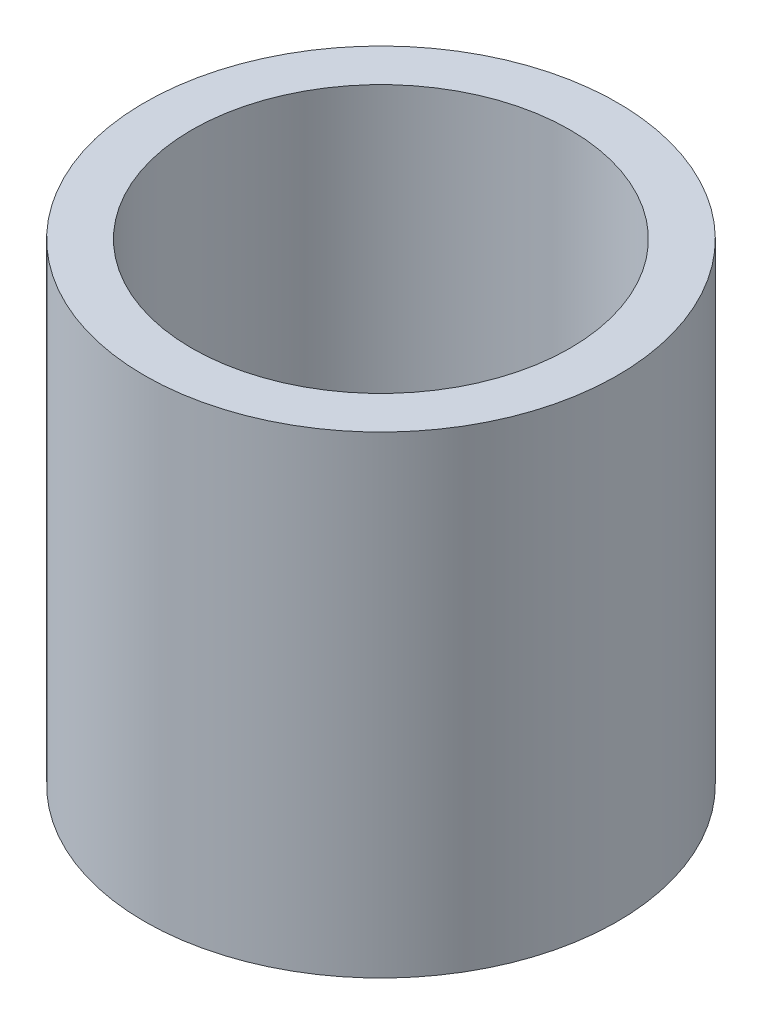
SolidWorks part; units mm, degrees
ref_plane "Front Plane" through (0, 0, 0) normal (0, 0, 1) x (1, 0, 0)
ref_plane "Top Plane" through (0, 0, 0) normal (0, 1, 0) x (1, 0, 0)
ref_plane "Right Plane" through (0, 0, 0) normal (1, 0, 0) x (0, 0, -1)
sketch "Sketch1" plane through (0, 0, 0) normal (0, 1, 0) x (1, 0, 0)
  circle A0 centre (-4.0593, 2.5534) radius 6.35
  dimension "D1" = 12.7
extrude "Boss-Extrude1" add sketch "Sketch1" along normal blind 12.7
sketch "Sketch2" plane through (0, 12.7, 0) normal (0, 1, 0) x (1, 0, 0)
  circle A0 centre (-4.0593, 2.5534) radius 5.08
extrude "Cut-Extrude1" cut sketch "Sketch2" against normal blind 13.716
